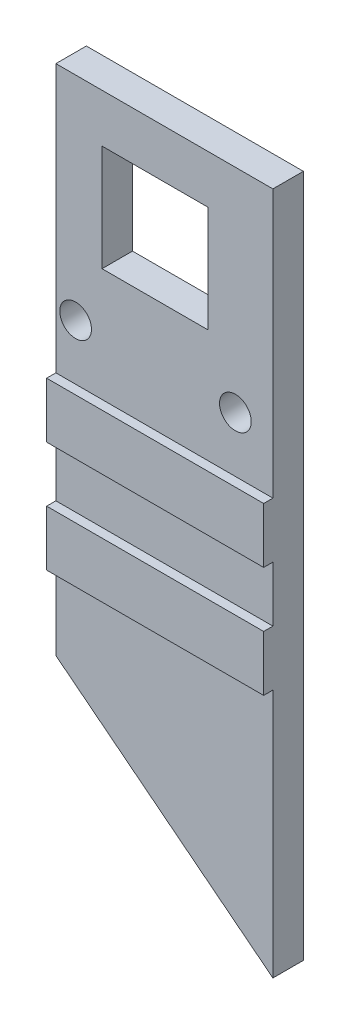
SolidWorks part; units mm, degrees
ref_plane "前基準面" through (0, 0, 0) normal (0, 0, 1) x (1, 0, 0)
ref_plane "上基準面" through (0, 0, 0) normal (0, 1, 0) x (1, 0, 0)
ref_plane "右基準面" through (0, 0, 0) normal (1, 0, 0) x (0, 0, -1)
sketch "草圖1" plane through (0, 0, 0) normal (0, 0, 1) x (1, 0, 0)
  line L1 (-15.254, 33.1662) -> (-15.254, -17.8338)
  line L2 (15.254, 33.1662) -> (15.254, -17.8338)
  line L4 (-5.7877, 27.9319) -> (5.7123, 27.9319)
  line L5 (-5.7877, 27.9319) -> (-5.7877, 19.0094)
  line L7 (5.7123, 27.9319) -> (5.7123, 19.0094)
  line L8 (0, 33.1662) -> (0, 8.7242) construction
  line L9 (-15.254, 2.1662) -> (15.254, 2.1662)
  line L10 (-15.254, 2.1662) -> (-15.254, -3.8338)
  line L11 (-15.254, -3.8338) -> (15.254, -3.8338)
  line L12 (15.254, 2.1662) -> (15.254, -3.8338)
  line L13 (-15.254, -11.8338) -> (15.254, -11.8338)
  line L14 (-15.254, -11.8338) -> (-15.254, -17.8338)
  line L15 (-15.254, -17.8338) -> (15.254, -17.8338)
  line L16 (15.254, -11.8338) -> (15.254, -17.8338)
  line L18 (-15.254, 33.1662) -> (-15.254, -17.8338)
  line L19 (-15.254, -17.8338) -> (15.254, -17.8338)
  line L20 (15.254, 33.1662) -> (15.254, -17.8338)
  line L21 (-15.254, -17.8338) -> (-15.254, -42.8338)
  line L23 (-5.7877, 19.0094) -> (-5.7877, 16.4319)
  line L24 (-5.7877, 16.4319) -> (5.7123, 16.4319)
  line L25 (5.7123, 19.0094) -> (5.7123, 16.4319)
  line L26 (-15.254, 33.1662) -> (15.254, 33.1662)
  line L27 (-15.254, -42.8338) -> (15.254, -42.8338)
  line L28 (15.254, -42.8338) -> (15.254, -17.8338)
  line L30 (-12.254, -20.8338) -> (12.254, -20.8338)
  line L31 (-12.254, -20.8338) -> (-12.254, -39.8338)
  line L32 (-12.254, -39.8338) -> (12.254, -39.8338)
  line L33 (12.254, -20.8338) -> (12.254, -39.8338)
  circle A0 centre (-8.65, 10.1662) radius 1.7161
  circle A1 centre (8.65, 10.1662) radius 1.7161
  dimension "D8" = 3
  dimension "D1" = 6
  dimension "D2" = 11.5
  dimension "D3" = 8
  dimension "D4" = 8
  dimension "D5" = 6
  dimension "D6" = 11.5
  dimension "D7" = 76
  dimension "D9" = 3
  dimension "D10" = 23
  dimension "D11" = 3
  dimension "D12" = 3
extrude "填料-伸長1" add sketch "草圖1" along normal blind 3.3 contours L8 L26 L1 L9 L24 L23 L5 L4 A0 | L26 L8 L4 L7 L25 L24 L9 L2 A1 | L8 L15 L21 L27 L32 L31 L30 | L19 L8 L30 L33 L32 L27 L28 | L8 L9 L1 L11 | L8 L13 L1 L15 | L13 L8 L19 L2 | L9 L8 L11 L2 | L8 L11 L1 L13 | L11 L8 L13 L2
sketch "草圖2" plane through (0, 0, 3.3) normal (0, 0, 1) x (1, 0, 0)
  line L0 (-15.254, 33.1662) -> (-15.254, -42.8338) construction
  line L1 (-15.254, 4.1662) -> (15.254, 4.1662)
  line L2 (-15.254, 4.1662) -> (-15.254, -1.8338)
  line L3 (-15.254, -1.8338) -> (15.254, -1.8338)
  line L4 (15.254, 4.1662) -> (15.254, -1.8338)
  line L5 (15.254, -42.8338) -> (15.254, 33.1662) construction
  line L7 (-15.254, -7.8338) -> (15.254, -7.8338)
  line L8 (-15.254, -7.8338) -> (-15.254, -13.8338)
  line L9 (-15.254, -13.8338) -> (15.254, -13.8338)
  line L10 (15.254, -7.8338) -> (15.254, -13.8338)
  circle A0 centre (-8.65, 10.1662) radius 1.7161 construction
  dimension "D1" = 6
  dimension "D2" = 6
  dimension "D3" = 6
  dimension "D4" = 6
extrude "填料-伸長2" add sketch "草圖2" along normal blind 1
sketch "草圖3" plane through (0, 0, 0) normal (0, 0, 1) x (1, 0, 0)
  line L0 (15.254, -42.8338) -> (-15.254, -18.4741)
  line L1 (-15.254, -13.8338) -> (-15.254, -42.8338) construction
  line L2 (-15.254, -18.4741) -> (15.254, -18.4741)
  line L3 (15.254, -42.8338) -> (15.254, -13.8338) construction
  line L4 (15.254, -18.4741) -> (15.254, -42.8338)
extrude "填料-伸長3" add sketch "草圖3" along normal blind 3.3
sketch "草圖4" plane through (0, 0, 3.3) normal (0, 0, 1) x (1, 0, 0)
  line L0 (15.254, -42.8338) -> (-15.254, -18.8067)
  line L1 (-15.254, -13.8338) -> (-15.254, -42.8338) construction
  line L2 (-15.254, -18.8067) -> (-15.254, -42.8338)
  line L3 (-15.254, -42.8338) -> (15.254, -42.8338)
extrude "除料-伸長1" cut sketch "草圖4" against normal blind 3.3
sketch "草圖5" plane through (0, 0, 3.3) normal (0, 0, 1) x (1, 0, 0)
  line L3 (15.254, -42.8338) -> (-15.254, -42.8338)
  line L4 (-15.254, -42.8338) -> (-15.254, -18.8067)
  line L5 (-15.254, -18.8067) -> (15.254, -42.8338)
extrude "填料-伸長5" add sketch "草圖5" against normal blind 3.3
sketch "草圖6" plane through (0, 0, 3.3) normal (0, 0, 1) x (1, 0, 0)
  line L0 (-15.254, -13.8338) -> (-15.254, -42.8338) construction
  line L1 (-15.254, -18.8067) -> (15.254, -18.8067)
  line L2 (-15.254, -18.8067) -> (-15.254, -42.8338)
  line L3 (-15.254, -42.8338) -> (15.254, -42.8338)
  line L4 (15.254, -18.8067) -> (15.254, -42.8338)
  line L5 (-15.254, -42.8338) -> (15.254, -42.8338) construction
extrude "填料-伸長6" add sketch "草圖6" against normal blind 3.3
sketch "草圖7" plane through (0, 0, 3.3) normal (0, 0, 1) x (1, 0, 0)
  line L0 (-15.254, -18.8338) -> (15.254, -42.8338)
  line L1 (-15.254, -13.8338) -> (-15.254, -42.8338) construction
  line L2 (-15.254, -18.8338) -> (-15.254, -42.8338)
  line L3 (-15.254, -42.8338) -> (15.254, -42.8338)
  dimension "D1" = 5
extrude "除料-伸長3" cut sketch "草圖7" against normal blind 3.3 contours L3 L0 L2
sketch "草圖8" plane through (0, 0, 4.3) normal (0, 0, 1) x (1, 0, 0)
  line L0 (-15.254, 33.1662) -> (15.254, 33.1662) construction
  line L1 (-15.254, 33.1662) -> (-10.7877, 33.1662)
  line L2 (-15.254, 33.1662) -> (-15.254, -24.906)
  line L3 (-15.254, -24.906) -> (-10.7877, -24.906)
  line L4 (-10.7877, 33.1662) -> (-10.7877, -24.906)
  line L5 (12.7123, 33.1662) -> (15.254, 33.1662)
  line L6 (12.7123, 33.1662) -> (12.7123, -42.8338)
  line L7 (12.7123, -42.8338) -> (15.254, -42.8338)
  line L8 (15.254, 33.1662) -> (15.254, -42.8338)
  line L9 (-5.7877, 27.9319) -> (-5.7877, 16.4319) construction
  line L10 (5.7123, 27.9319) -> (5.7123, 16.4319) construction
  dimension "D1" = 5
  dimension "D2" = 7
extrude "除料-伸長4" cut sketch "草圖8" against normal blind 11.3
